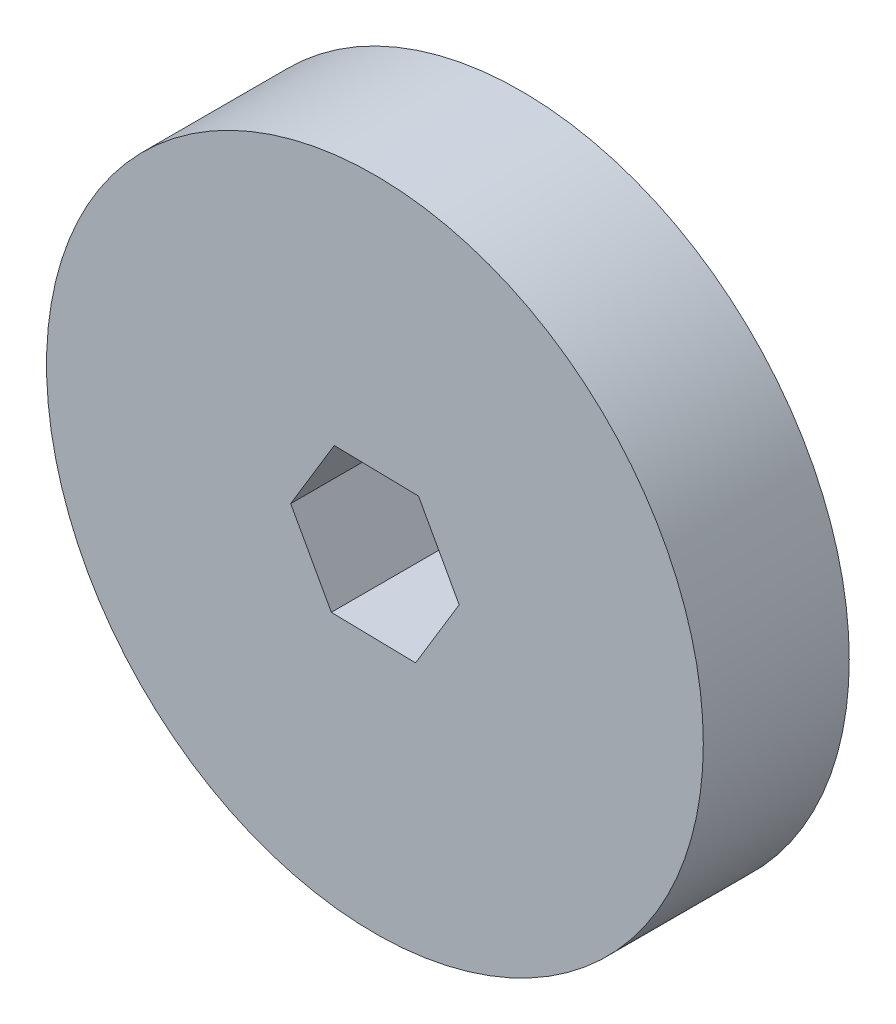
SolidWorks part; units mm, degrees
ref_plane "Front Plane" through (0, 0, 0) normal (0, 0, 1) x (1, 0, 0)
ref_plane "Top Plane" through (0, 0, 0) normal (0, 1, 0) x (1, 0, 0)
ref_plane "Right Plane" through (0, 0, 0) normal (1, 0, 0) x (0, 0, -1)
sketch "Sketch1" plane through (0, 0, 0) normal (0, 0, 1) x (1, 0, 0)
  line L1 (3.5382, -6.4222) -> (7.3309, -0.147)
  line L2 (7.3309, -0.147) -> (3.7927, 6.2752)
  line L3 (3.7927, 6.2752) -> (-3.5382, 6.4222)
  line L4 (-3.5382, 6.4222) -> (-7.3309, 0.147)
  line L5 (-7.3309, 0.147) -> (-3.7927, -6.2752)
  line L6 (-3.7927, -6.2752) -> (3.5382, -6.4222)
  circle A0 centre (0, 0) radius 28.575
  circle A1 centre (0, 0) radius 6.35 construction
  dimension "D1" = 57.15
  dimension "D2" = 12.7
extrude "Boss-Extrude1" add sketch "Sketch1" along normal blind 12.7
